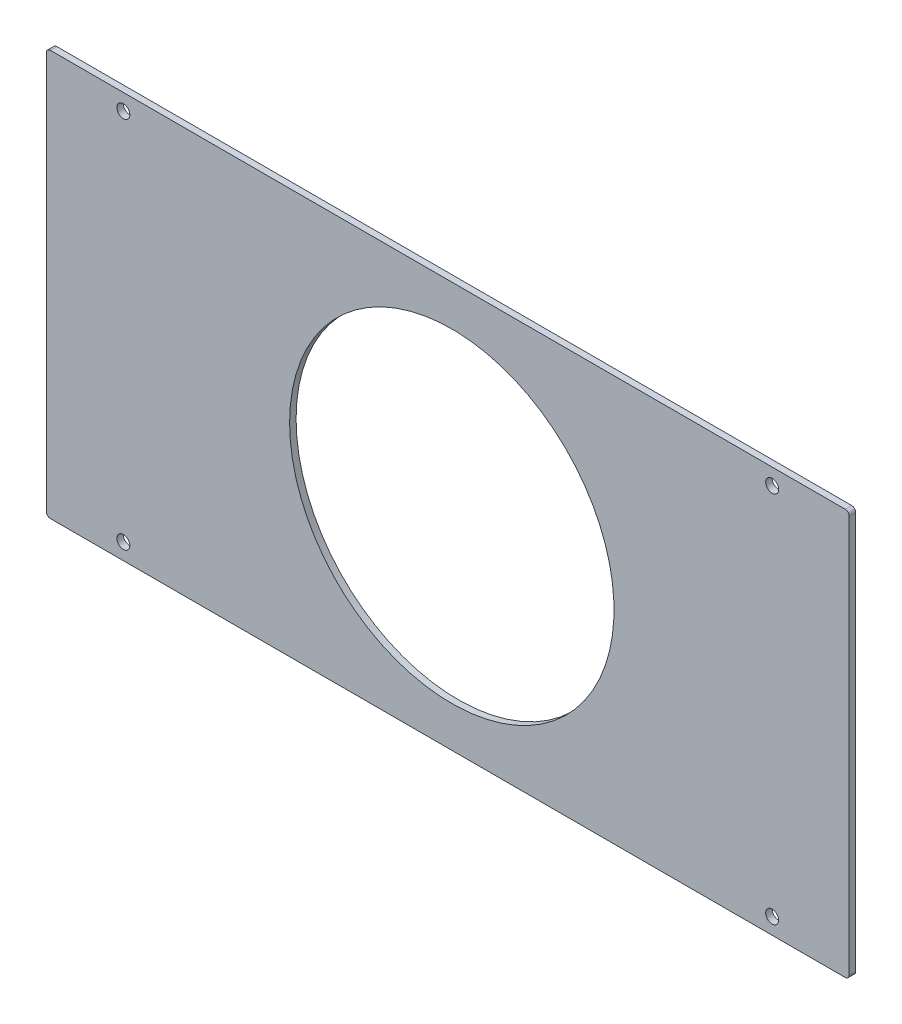
SolidWorks part; units mm, degrees
material "Epoxy, renforcé"
ref_plane "Plan de face" through (0, 0, 0) normal (0, 0, 1) x (1, 0, 0)
ref_plane "Plan de dessus" through (0, 0, 0) normal (0, 1, 0) x (1, 0, 0)
ref_plane "Plan de droite" through (0, 0, 0) normal (1, 0, 0) x (0, 0, -1)
sketch "Esquisse1" plane through (0, 0, 0) normal (0, 0, 1) x (1, 0, 0)
  line L1 (1, 0) -> (197, 0)
  line L2 (0, 1) -> (0, 99)
  line L3 (1, 100) -> (197, 100)
  line L4 (198, 1) -> (198, 99)
  arc A0 (197, 100) -> (198, 99) centre (197, 99) cw
  arc A1 (197, 0) -> (198, 1) centre (197, 1) ccw
  arc A2 (1, 0) -> (0, 1) centre (1, 1) cw
  arc A3 (0, 99) -> (1, 100) centre (1, 99) cw
  point P10 (198, 0)
  point P13 (0, 0)
  point P16 (0, 100)
  dimension "D3" = 1
  dimension "D1" = 198
  dimension "D2" = 100
extrude "Boss.-Extru.1" add sketch "Esquisse1" along normal blind 1.6
sketch "Esquisse3" plane through (0, 0, 0) normal (0, 0, -1) x (-1, 0, 0)
  line L0 (0, 99) -> (0, 1) construction
  line L1 (-198, 1) -> (-198, 99) construction
  line L2 (-197, 100) -> (-1, 100) construction
  line L3 (-1, 0) -> (-197, 0) construction
  circle A0 centre (-179, 96) radius 1.6
  circle A1 centre (-179, 4) radius 1.6
  circle A2 centre (-19, 4) radius 1.6
  circle A3 centre (-19, 96) radius 1.6
  circle A4 centre (-100, 50) radius 40
  dimension "D1" = 19
  dimension "D9" = 80
  dimension "D2" = 19
  dimension "D3" = 19
  dimension "D4" = 19
  dimension "D5" = 4
  dimension "D6" = 4
  dimension "D7" = 4
  dimension "D8" = 4
extrude "Enlèv. mat.-Extru.1" cut sketch "Esquisse3" against normal through all
sketch "Esquisse2" plane through (0, 0, 0) normal (0, 0, -1) x (-1, 0, 0)
  line L0 (-162.7686, 50) -> (-56.7804, 50) construction
  line L1 (-110, 94.4248) -> (-110, 2.4181) construction
  line L2 (-110, 50) -> (-57.212, 59.3079) construction
  circle A0 centre (-110, 50) radius 30
  circle A1 centre (-110, 50) radius 35
  circle A2 centre (-110, 50) radius 40
  circle A4 centre (-110, 50) radius 25
  dimension "D1" = 10
